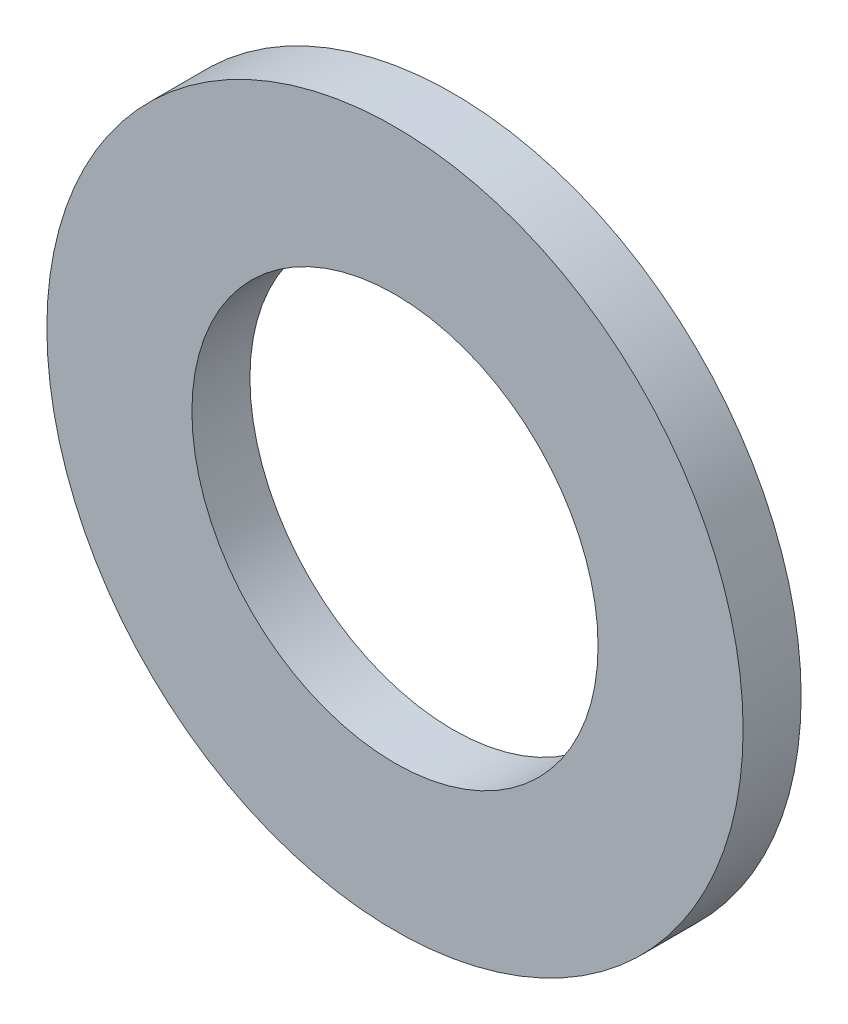
SolidWorks part; units mm, degrees
ref_plane "前视基准面" through (0, 0, 0) normal (0, 0, 1) x (1, 0, 0)
ref_plane "上视基准面" through (0, 0, 0) normal (0, 1, 0) x (1, 0, 0)
ref_plane "右视基准面" through (0, 0, 0) normal (1, 0, 0) x (0, 0, -1)
other "Configuration Table"
sketch "草图1" plane through (0, 0, 0) normal (0, 0, 1) x (1, 0, 0)
  circle A0 centre (0, 0) radius 8.75
  circle A1 centre (0, 0) radius 15
  dimension "D1" = 17.5
  dimension "D2" = 30
extrude "凸台-拉伸1" add sketch "草图1" along normal blind 2.5
